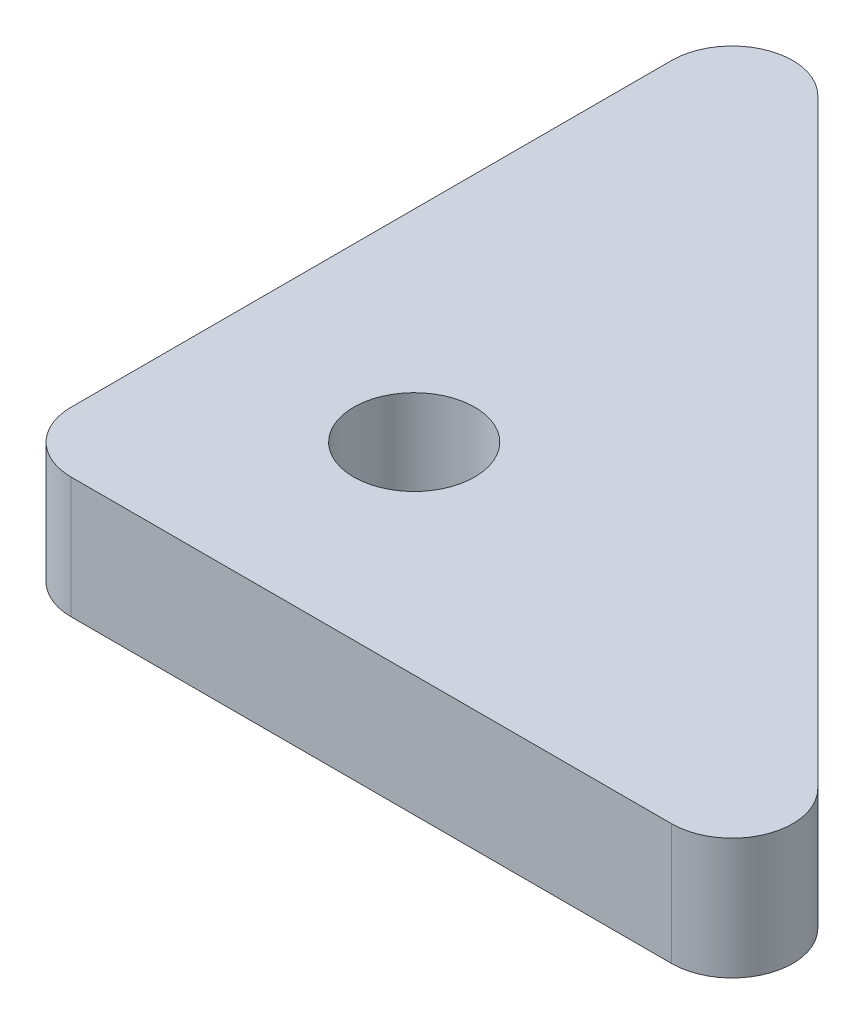
SolidWorks part; units mm, degrees
material "Plain Carbon Steel"
ref_plane "Front Plane" through (0, 0, 0) normal (0, 0, 1) x (1, 0, 0)
ref_plane "Top Plane" through (0, 0, 0) normal (0, 1, 0) x (1, 0, 0)
ref_plane "Right Plane" through (0, 0, 0) normal (1, 0, 0) x (0, 0, -1)
sketch "Sketch1" plane through (0, 0, 0) normal (0, 1, 0) x (1, 0, 0)
  line L0 (5.1213, 34.8787) -> (34.8787, 5.1213)
  line L1 (3, 0) -> (32.7574, 0)
  line L2 (0, 3) -> (0, 32.7574)
  line L5 (10, 10) -> (10, 40) construction
  line L6 (10, 10) -> (40, 10) construction
  line L7 (0, 0) -> (40, 0) construction
  line L8 (0, 0) -> (0, 40) construction
  circle A0 centre (10, 10) radius 3
  arc A1 (3, 0) -> (0, 3) centre (3, 3) cw
  arc A2 (32.7574, 0) -> (34.8787, 5.1213) centre (32.7574, 3) ccw
  arc A3 (0, 32.7574) -> (5.1213, 34.8787) centre (3, 32.7574) cw
  point P11 (0, 0)
  dimension "D4" = 3
  dimension "D3" = 10
extrude "Boss-Extrude1" add sketch "Sketch1" along normal blind 6
